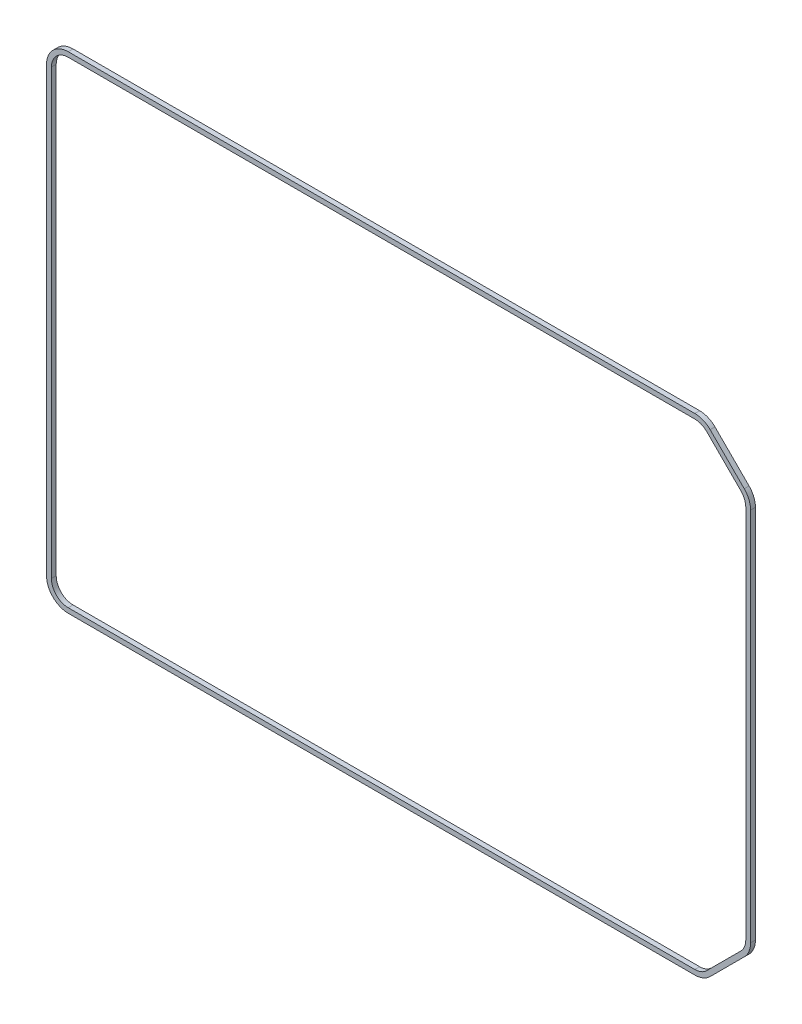
SolidWorks part; units mm, degrees
ref_plane "Front Plane" through (0, 0, 0) normal (0, 0, 1) x (1, 0, 0)
ref_plane "Top Plane" through (0, 0, 0) normal (0, 1, 0) x (1, 0, 0)
ref_plane "Right Plane" through (0, 0, 0) normal (1, 0, 0) x (0, 0, -1)
sketch "Sketch1" plane through (0, 0, 0) normal (0, 0, 1) x (1, 0, 0)
  line L18 (64.6059, -49.107) -> (71.677, -42.0359) construction
  line L19 (72.995, -38.8539) -> (72.995, 38.8539) construction
  line L20 (71.677, 42.0359) -> (64.6059, 49.107) construction
  line L21 (61.4239, 50.425) -> (-68.495, 50.425) construction
  line L22 (-72.995, 45.925) -> (-72.995, -45.925) construction
  line L23 (-68.495, -50.425) -> (61.4239, -50.425) construction
  line L24 (-71.995, 45.925) -> (-71.995, -45.925)
  line L25 (-72.995, -45.925) -> (-72.995, 45.925)
  line L26 (-68.495, 50.425) -> (61.4239, 50.425)
  line L27 (64.6059, 49.107) -> (71.677, 42.0359)
  line L28 (72.995, 38.8539) -> (72.995, -38.8539)
  line L29 (71.677, -42.0359) -> (64.6059, -49.107)
  line L36 (63.8988, -48.3999) -> (70.9699, -41.3288) construction
  line L37 (71.995, -38.8539) -> (71.995, 38.8539) construction
  line L38 (70.9699, 41.3288) -> (63.8988, 48.3999) construction
  line L39 (61.4239, 49.425) -> (-68.495, 49.425) construction
  line L40 (-71.995, 45.925) -> (-71.995, -45.925) construction
  line L41 (-68.495, -49.425) -> (61.4239, -49.425) construction
  line L42 (-68.495, -50.425) -> (61.4239, -50.425)
  line L43 (70.9699, -41.3288) -> (63.8988, -48.3999)
  line L44 (61.4239, -49.425) -> (-68.495, -49.425)
  line L45 (71.995, 38.8539) -> (71.995, -38.8539)
  line L46 (63.8988, 48.3999) -> (70.9699, 41.3288)
  line L47 (61.4239, 49.425) -> (-68.495, 49.425)
  arc A18 (61.4239, -50.425) -> (64.6059, -49.107) centre (61.4239, -45.925) ccw construction
  arc A19 (71.677, -42.0359) -> (72.995, -38.8539) centre (68.495, -38.8539) ccw construction
  arc A20 (72.995, 38.8539) -> (71.677, 42.0359) centre (68.495, 38.8539) ccw construction
  arc A21 (64.6059, 49.107) -> (61.4239, 50.425) centre (61.4239, 45.925) ccw construction
  arc A22 (-68.495, 50.425) -> (-72.995, 45.925) centre (-68.495, 45.925) ccw construction
  arc A23 (-72.995, -45.925) -> (-68.495, -50.425) centre (-68.495, -45.925) ccw construction
  arc A24 (-71.995, 45.925) -> (-68.495, 49.425) centre (-68.495, 45.925) cw
  arc A25 (-72.995, 45.925) -> (-68.495, 50.425) centre (-68.495, 45.925) cw
  arc A26 (61.4239, 49.425) -> (63.8988, 48.3999) centre (61.4239, 45.925) cw
  arc A27 (61.4239, 50.425) -> (64.6059, 49.107) centre (61.4239, 45.925) cw
  arc A28 (70.9699, 41.3288) -> (71.995, 38.8539) centre (68.495, 38.8539) cw
  arc A29 (71.677, 42.0359) -> (72.995, 38.8539) centre (68.495, 38.8539) cw
  arc A36 (61.4239, -49.425) -> (63.8988, -48.3999) centre (61.4239, -45.925) ccw construction
  arc A37 (70.9699, -41.3288) -> (71.995, -38.8539) centre (68.495, -38.8539) ccw construction
  arc A38 (71.995, 38.8539) -> (70.9699, 41.3288) centre (68.495, 38.8539) ccw construction
  arc A39 (63.8988, 48.3999) -> (61.4239, 49.425) centre (61.4239, 45.925) ccw construction
  arc A40 (-68.495, 49.425) -> (-71.995, 45.925) centre (-68.495, 45.925) ccw construction
  arc A41 (-71.995, -45.925) -> (-68.495, -49.425) centre (-68.495, -45.925) ccw construction
  arc A42 (71.995, -38.8539) -> (70.9699, -41.3288) centre (68.495, -38.8539) cw
  arc A43 (72.995, -38.8539) -> (71.677, -42.0359) centre (68.495, -38.8539) cw
  arc A44 (63.8988, -48.3999) -> (61.4239, -49.425) centre (61.4239, -45.925) cw
  arc A45 (64.6059, -49.107) -> (61.4239, -50.425) centre (61.4239, -45.925) cw
  arc A46 (-68.495, -49.425) -> (-71.995, -45.925) centre (-68.495, -45.925) cw
  arc A47 (-68.495, -50.425) -> (-72.995, -45.925) centre (-68.495, -45.925) cw
extrude "Boss-Extrude1" add sketch "Sketch1" along normal blind 1
